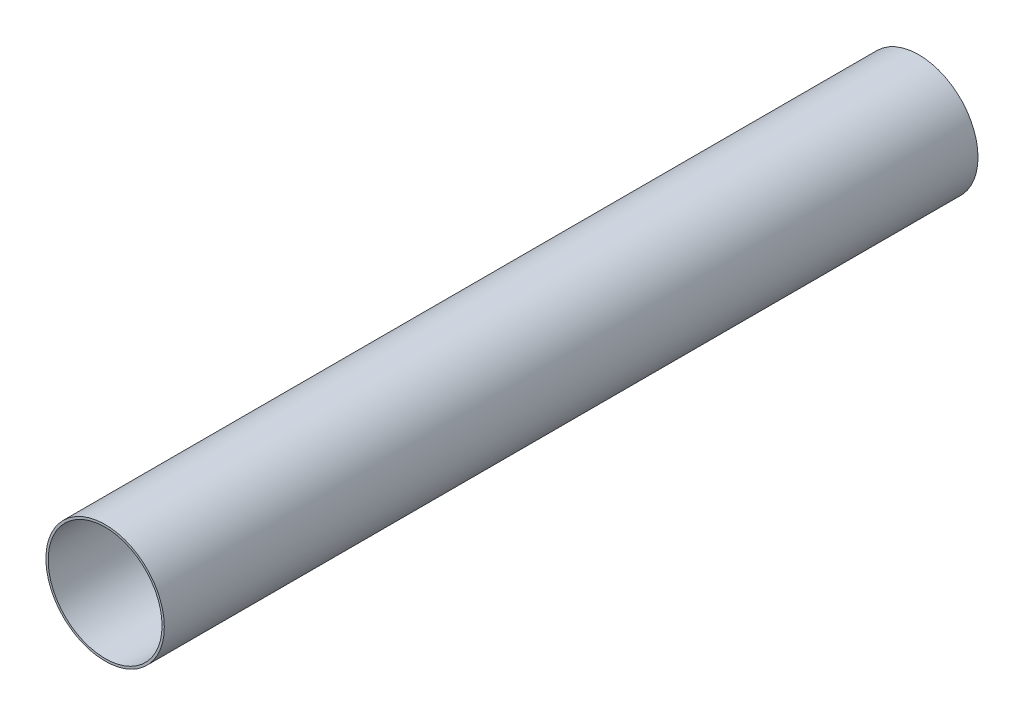
SolidWorks part; units mm, degrees
ref_plane "Front Plane" through (0, 0, 0) normal (0, 0, 1) x (1, 0, 0)
ref_plane "Top Plane" through (0, 0, 0) normal (0, 1, 0) x (1, 0, 0)
ref_plane "Right Plane" through (0, 0, 0) normal (1, 0, 0) x (0, 0, -1)
sketch "Sketch1" plane through (0, 0, 0) normal (0, 0, 1) x (1, 0, 0)
  circle A0 centre (0, 0) radius 38.1
  circle A1 centre (0, 0) radius 39.624
  dimension "D1" = 76.2
  dimension "D2" = 79.248
extrude "Boss-Extrude1" add sketch "Sketch1" along normal blind 544.5125
